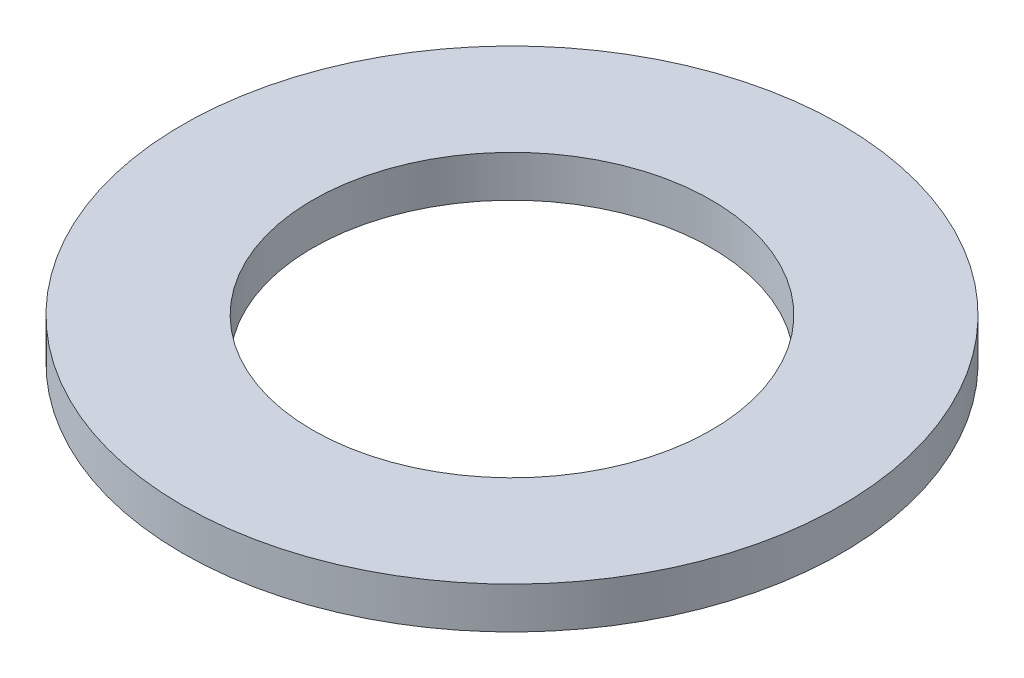
SolidWorks part; units mm, degrees
ref_plane "Front Plane" through (0, 0, 0) normal (0, 0, 1) x (1, 0, 0)
ref_plane "Top Plane" through (0, 0, 0) normal (0, 1, 0) x (1, 0, 0)
ref_plane "Right Plane" through (0, 0, 0) normal (1, 0, 0) x (0, 0, -1)
sketch "Sketch1" plane through (0, 0, 0) normal (0, 1, 0) x (1, 0, 0)
  circle A0 centre (0, 0) radius 15.748
  dimension "D1" = 31.496
extrude "Boss-Extrude1" add sketch "Sketch1" along normal blind 1.9812
sketch "Sketch2" plane through (0, 1.9812, 0) normal (0, 1, 0) x (1, 0, 0)
  circle A0 centre (0, 0) radius 9.525
  dimension "D1" = 19.05
extrude "Cut-Extrude1" cut sketch "Sketch2" against normal blind 4.5212
